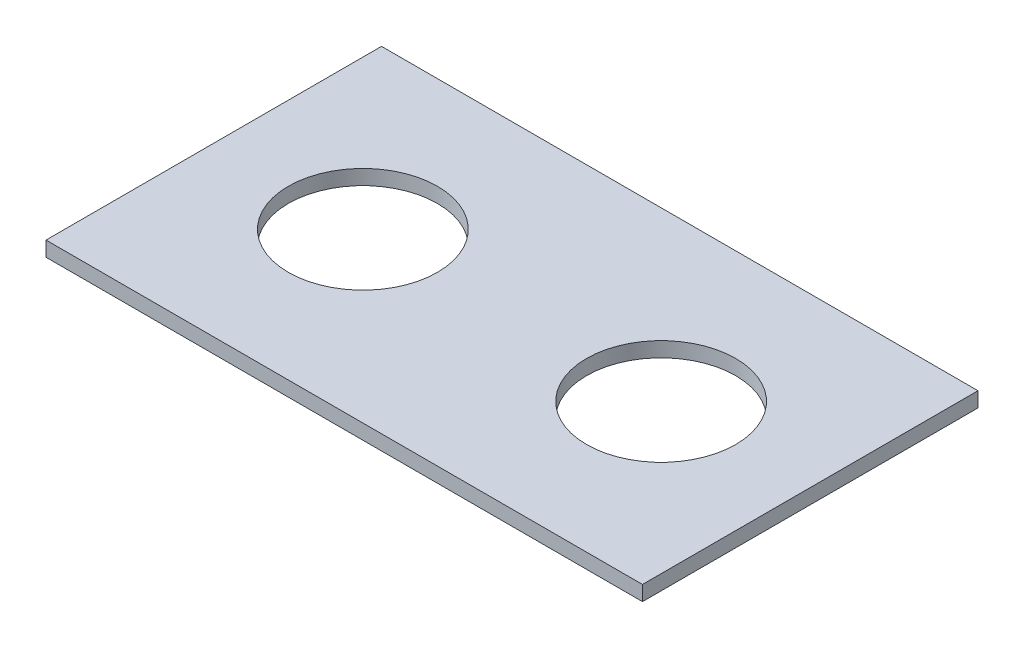
SolidWorks part; units mm, degrees
ref_plane "Front Plane" through (0, 0, 0) normal (0, 0, 1) x (1, 0, 0)
ref_plane "Top Plane" through (0, 0, 0) normal (0, 1, 0) x (1, 0, 0)
ref_plane "Right Plane" through (0, 0, 0) normal (1, 0, 0) x (0, 0, -1)
sketch "Sketch1" plane through (0, 0, 0) normal (0, 1, 0) x (1, 0, 0)
  line L1 (-50.8, -28.575) -> (50.8, -28.575)
  line L2 (-50.8, -28.575) -> (-50.8, 28.575)
  line L3 (-50.8, 28.575) -> (50.8, 28.575)
  line L4 (50.8, -28.575) -> (50.8, 28.575)
  line L5 (-50.8, -28.575) -> (50.8, 28.575) construction
  line L6 (-50.8, 28.575) -> (50.8, -28.575) construction
  point P0 (0, 0)
  dimension "D1" = 101.6
  dimension "D2" = 57.15
extrude "Boss-Extrude1" add sketch "Sketch1" along normal blind 2.54 contours L2 L3 L4 L1
sketch "Sketch2" plane through (0, 2.54, 0) normal (0, 1, 0) x (1, 0, 0)
  line L0 (-50.8, -28.575) -> (-50.8, 28.575) construction
  line L1 (-50.8, 28.575) -> (50.8, 28.575) construction
  line L2 (0, -1.397) -> (0, 1.397) construction
  circle A0 centre (-25.4, 0) radius 12.7
  circle A1 centre (25.4, 0) radius 12.7
  dimension "D1" = 25.4
  dimension "D2" = 25.4
  dimension "D3" = 28.575
extrude "Cut-Extrude1" cut sketch "Sketch2" against normal blind 2.54
